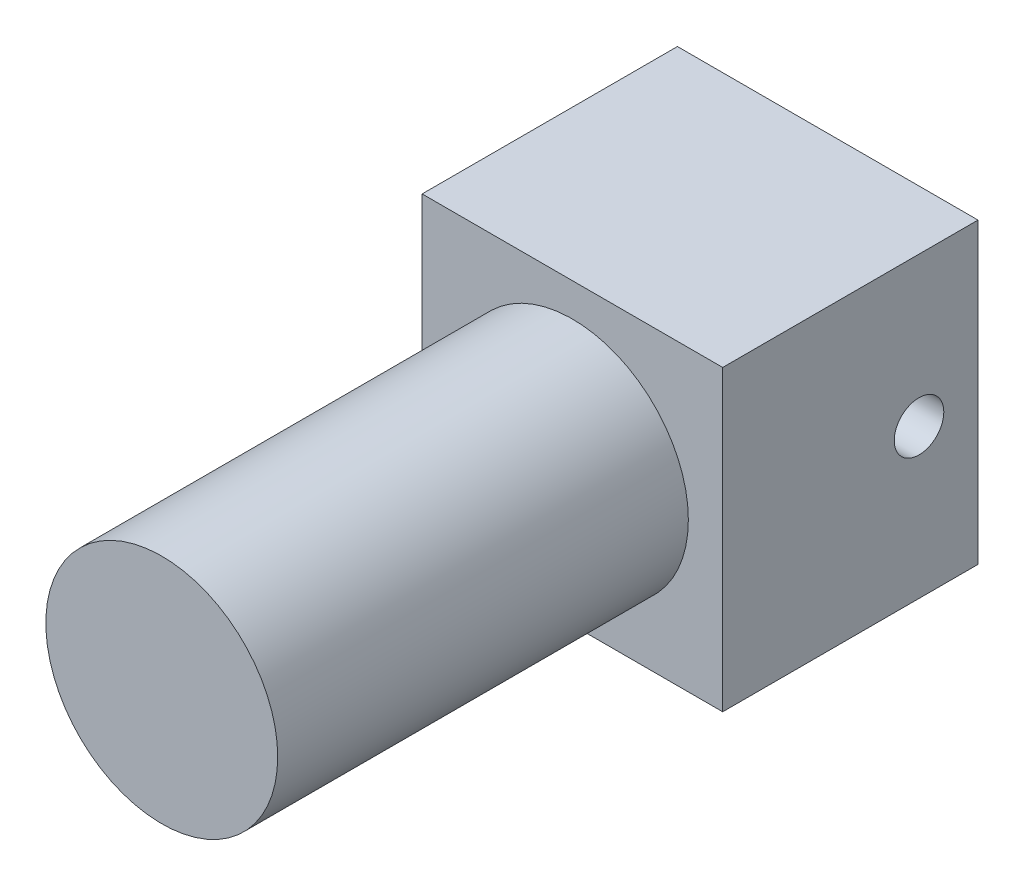
SolidWorks part; units mm, degrees
ref_plane "Front Plane" through (0, 0, 0) normal (0, 0, 1) x (1, 0, 0)
ref_plane "Top Plane" through (0, 0, 0) normal (0, 1, 0) x (1, 0, 0)
ref_plane "Right Plane" through (0, 0, 0) normal (1, 0, 0) x (0, 0, -1)
sketch "Sketch1" plane through (0, 0, 0) normal (0, 0, 1) x (1, 0, 0)
  line L1 (-19.25, -19.1) -> (19.25, -19.1)
  line L2 (-19.25, -19.1) -> (-19.25, 19.1)
  line L3 (-19.25, 19.1) -> (19.25, 19.1)
  line L4 (19.25, -19.1) -> (19.25, 19.1)
  line L5 (-19.25, -19.1) -> (19.25, 19.1) construction
  line L6 (-19.25, 19.1) -> (19.25, -19.1) construction
  point P0 (0, 0)
  dimension "D1" = 38.5
  dimension "D2" = 38.2
extrude "Boss-Extrude1" add sketch "Sketch1" along normal blind 32.7
sketch "Sketch2" plane through (0, 0, 32.7) normal (0, 0, 1) x (1, 0, 0)
  circle A0 centre (0, 0) radius 14.85
  dimension "D1" = 29.7
extrude "Boss-Extrude2" add sketch "Sketch2" along normal blind 52.6
sketch "Sketch3" plane through (19.25, 0, 0) normal (1, 0, 0) x (0, 0, -1)
  circle A0 centre (-7.5543, 0) radius 3.175
  dimension "D1" = 6.35
extrude "Cut-Extrude1" cut sketch "Sketch3" against normal blind 7.2136 contours A0
mirror "Mirror1" about plane through (0, 0, 0) normal (1, 0, 0) of "Cut-Extrude1"
sketch "Sketch4" plane through (0, 0, 0) normal (0, 0, -1) x (-1, 0, 0)
  circle A0 centre (0, -16.6516) radius 2.066
extrude "Boss-Extrude3" add sketch "Sketch4" along normal blind 5.08
